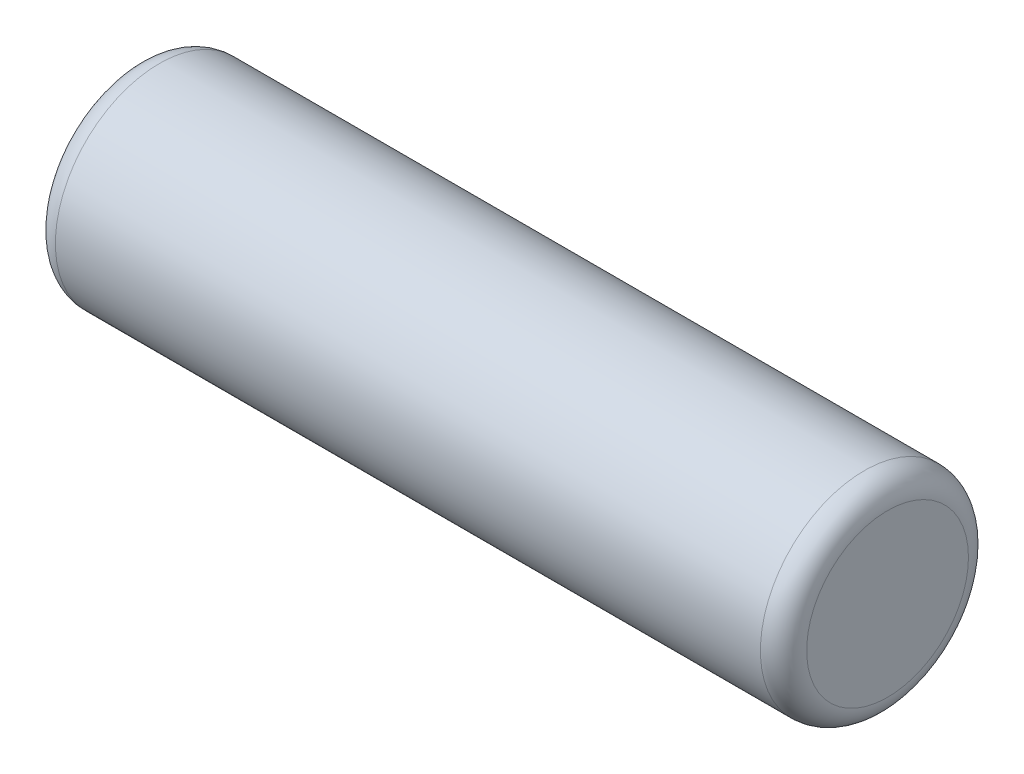
SolidWorks part; units mm, degrees
ref_plane "Front Plane" through (0, 0, 0) normal (0, 0, 1) x (1, 0, 0)
ref_plane "Top Plane" through (0, 0, 0) normal (0, 1, 0) x (1, 0, 0)
ref_plane "Right Plane" through (0, 0, 0) normal (1, 0, 0) x (0, 0, -1)
sketch "Sketch1" plane through (0, 0, 0) normal (1, 0, 0) x (0, 0, -1)
  circle A0 centre (0, 0) radius 9
  dimension "D1" = 18
extrude "Boss-Extrude1" add sketch "Sketch1" along normal mid plane 65
fillet "Fillet1" radius 2 2 edges at (-32.5, 0, -9) (32.5, 0, -9)
